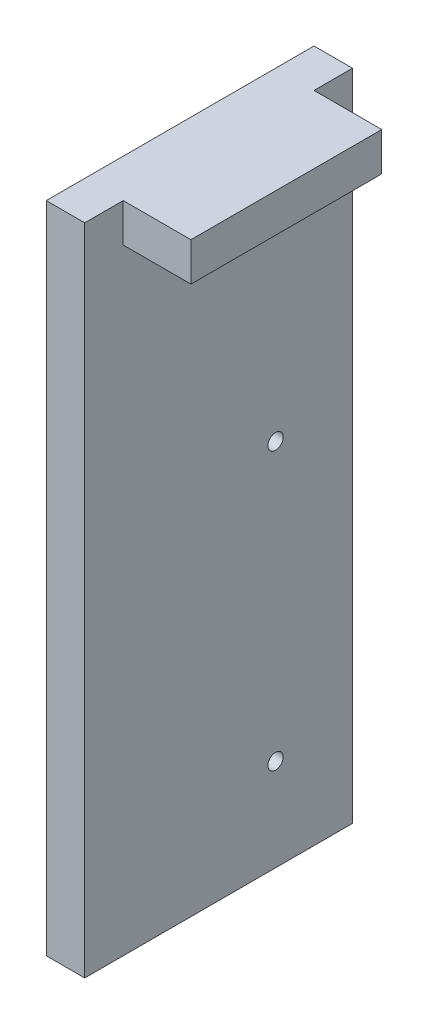
SolidWorks part; units mm, degrees
ref_plane "Front Plane" through (0, 0, 0) normal (0, 0, 1) x (1, 0, 0)
ref_plane "Top Plane" through (0, 0, 0) normal (0, 1, 0) x (1, 0, 0)
ref_plane "Right Plane" through (0, 0, 0) normal (1, 0, 0) x (0, 0, -1)
sketch "Sketch1" plane through (0, 0, 0) normal (1, 0, 0) x (0, 0, -1)
  line L1 (-5.5245, 13.4938) -> (5.5245, 13.4938)
  line L2 (-5.5245, 13.4938) -> (-5.5245, -13.4937)
  line L3 (-5.5245, -13.4937) -> (5.5245, -13.4937)
  line L4 (5.5245, 13.4938) -> (5.5245, -13.4937)
  line L5 (-5.5245, 13.4938) -> (5.5245, -13.4937) construction
  line L6 (-5.5245, -13.4937) -> (5.5245, 13.4938) construction
  point P0 (0, 0)
  dimension "D1" = 11.049
  dimension "D2" = 26.9875
extrude "Boss-Extrude1" add sketch "Sketch1" along normal blind 1.5875
sketch "Sketch2" plane through (1.5875, 0, 0) normal (1, 0, 0) x (0, 0, -1)
  line L0 (5.5245, 13.4938) -> (-5.5245, 13.4938) construction
  line L1 (-3.937, 13.4938) -> (3.937, 13.4938)
  line L2 (-3.937, 13.4938) -> (-3.937, 11.9062)
  line L3 (-3.937, 11.9062) -> (3.937, 11.9062)
  line L4 (3.937, 13.4938) -> (3.937, 11.9062)
  line L5 (-3.937, 13.4938) -> (3.937, 11.9062) construction
  line L6 (-3.937, 11.9062) -> (3.937, 13.4938) construction
  line L7 (5.5245, -13.4937) -> (5.5245, 13.4938) construction
  line L8 (-5.5245, 13.4938) -> (-5.5245, -13.4937) construction
  point P0 (0, 12.7)
  dimension "D1" = 1.5875
  dimension "D2" = 1.5875
  dimension "D3" = 1.5875
extrude "Boss-Extrude2" add sketch "Sketch2" along normal blind 2.794
sketch "Sketch3" plane through (0, 0, 0) normal (-1, 0, 0) x (0, 0, 1)
  line L0 (5.5245, -13.4937) -> (-5.5245, -13.4937) construction
  line L1 (-5.5245, -13.4937) -> (-5.5245, 13.4938) construction
  circle A0 centre (-2.3495, 1.7463) radius 0.3175
  circle A1 centre (-2.3495, -9.6837) radius 0.3175
  point P8 (0, 0)
  point P9 (-3.6195, -2.4588)
  dimension "D1" = 3.81
  dimension "D2" = 0.635
  dimension "D3" = 3.175
  dimension "D4" = 11.43
extrude "Cut-Extrude1" cut sketch "Sketch3" against normal up to next
